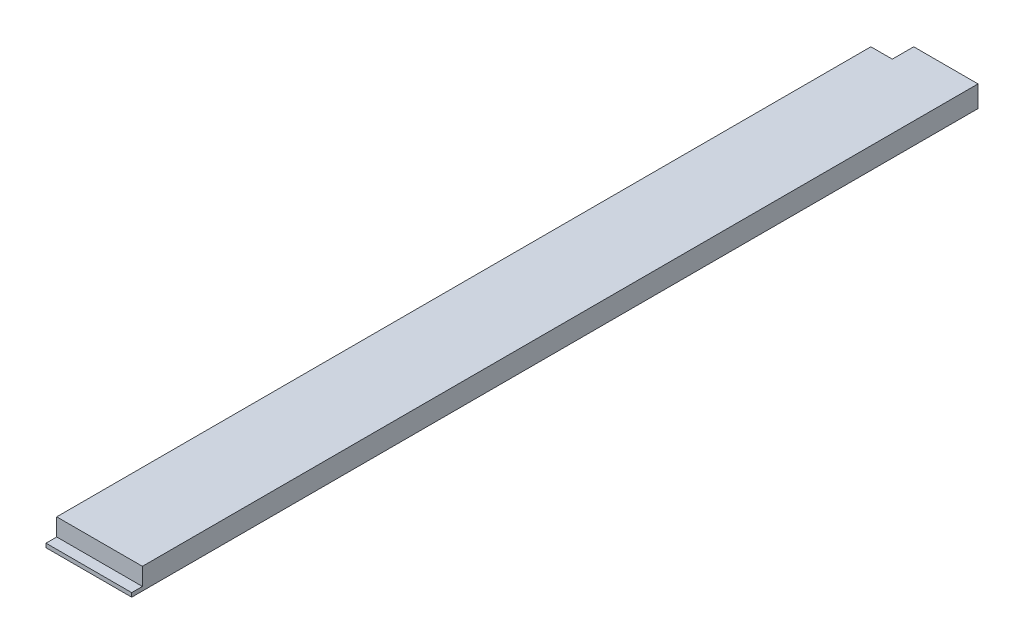
SolidWorks part; units mm, degrees
ref_plane "Front Plane" through (0, 0, 0) normal (0, 0, 1) x (1, 0, 0)
ref_plane "Top Plane" through (0, 0, 0) normal (0, 1, 0) x (1, 0, 0)
ref_plane "Right Plane" through (0, 0, 0) normal (1, 0, 0) x (0, 0, -1)
sketch "Sketch1" plane through (0, 0, 0) normal (0, 0, 1) x (1, 0, 0)
  line L0 (0, 12.7) -> (0, 6.35)
  line L3 (12.7, 0) -> (50.8, 0)
  line L4 (50.8, 0) -> (50.8, 12.7)
  line L5 (50.8, 12.7) -> (0, 12.7)
  line L6 (12.7, 0) -> (0, 0)
  line L7 (0, 0) -> (0, 6.35)
  dimension "D1" = 6.35
  dimension "D4" = 50.8
extrude "Boss-Extrude1" add sketch "Sketch1" along normal blind 501.65
sketch "Sketch2" plane through (0, 12.7, 0) normal (0, -1, 0) x (1, 0, 0)
  line L5 (50.8, 501.65) -> (50.8, 0) construction
  line L7 (50.8, 495.3) -> (0, 495.3)
  line L8 (50.8, 495.3) -> (50.8, 501.65)
  line L9 (50.8, 501.65) -> (0, 501.65)
  line L10 (0, 495.3) -> (0, 501.65)
  dimension "D1" = 6.35
extrude "Cut-Extrude1" cut sketch "Sketch2" along normal blind 10.3378
sketch "Sketch3" plane through (0, 12.7, 0) normal (0, 1, 0) x (1, 0, 0)
  line L1 (0, 0) -> (12.7, 0)
  line L2 (0, 0) -> (0, -12.7)
  line L3 (0, -12.7) -> (12.7, -12.7)
  line L4 (12.7, 0) -> (12.7, -12.7)
  dimension "D1" = 12.7
  dimension "D2" = 12.7
extrude "Cut-Extrude2" cut sketch "Sketch3" against normal through all
